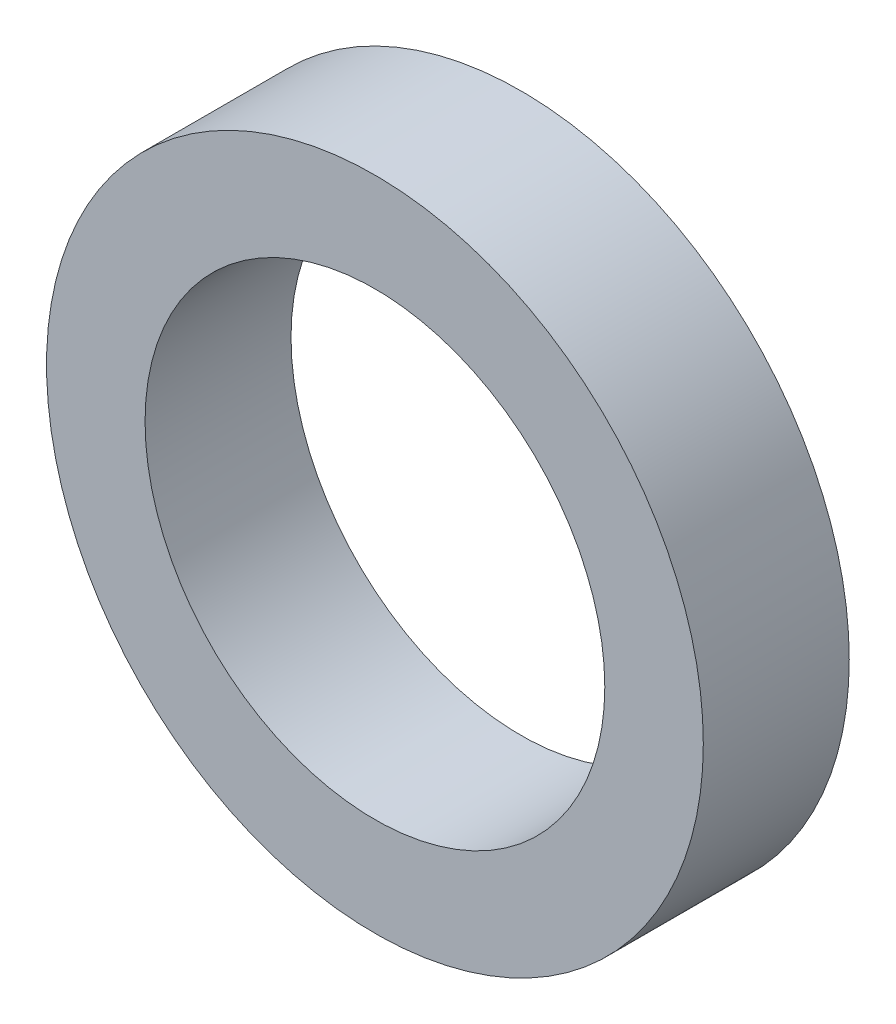
SolidWorks part; units mm, degrees
material "Ст 3 ГОСТ 380-2005"
ref_plane "Спереди" through (0, 0, 0) normal (0, 0, 1) x (1, 0, 0)
ref_plane "Сверху" through (0, 0, 0) normal (0, 1, 0) x (1, 0, 0)
ref_plane "Слева" through (0, 0, 0) normal (1, 0, 0) x (0, 0, -1)
sketch "Эскиз1" plane through (0, 0, 0) normal (0, 0, 1) x (1, 0, 0)
  circle A0 centre (0, 0) radius 15.75
  circle A1 centre (0, 0) radius 22.5
  dimension "D1" = 31.5
  dimension "D2" = 45
extrude "Вытянуть1" add sketch "Эскиз1" along normal blind 10
